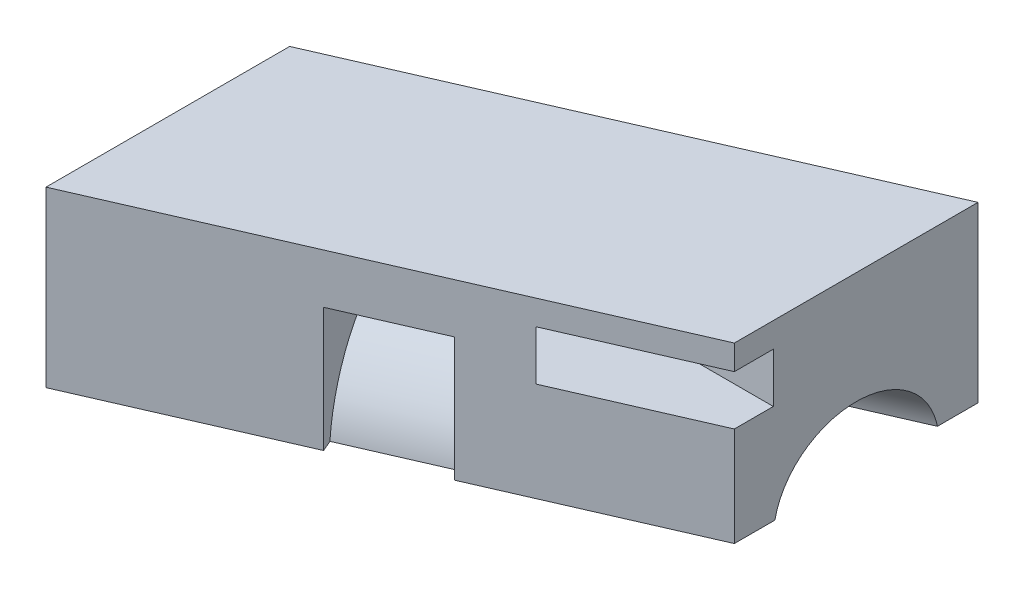
SolidWorks part; units mm, degrees
ref_plane "Front Plane" through (0, 0, 0) normal (0, 0, 1) x (1, 0, 0)
ref_plane "Top Plane" through (0, 0, 0) normal (0, 1, 0) x (1, 0, 0)
ref_plane "Right Plane" through (0, 0, 0) normal (1, 0, 0) x (0, 0, -1)
sketch "Sketch2" plane through (0, 0, 0) normal (0, 1, 0) x (1, 0, 0)
  line L0 (0, 0) -> (-3.6, 8.2486)
  line L1 (-3.6, 8.2486) -> (19.3129, 18.2486)
  line L2 (19.3129, 18.2486) -> (22.9129, 10)
  line L3 (22.9129, 10) -> (0, 0)
  dimension "D1" = 25
  dimension "D2" = 9
  dimension "D3" = 10
extrude "Boss-Extrude2" add sketch "Sketch2" along normal blind 7
sketch "Sketch4" plane through (0, 0, 0) normal (-0.9165, 0, 0.4) x (0.4, 0, 0.9165)
  line L1 (-9, 4.5) -> (0, 4.5) construction
  line L2 (-9, 7) -> (-9, 0) construction
  line L4 (0, 7) -> (0, 0) construction
  line L6 (-9, 7) -> (0, 7) construction
  line L7 (-7.5, 7) -> (-1.5, 7)
  arc A0 (-7.5, 7) -> (-1.5, 7) centre (-4.5, 7.55) ccw
  dimension "D1" = 1.5
  dimension "D2" = 2.5
  dimension "D3" = 1.5
extrude "Cut-Extrude4" cut sketch "Sketch4" against normal up to surface (25 mm away) up to face at (21.1129, 3.5, -14.1243)
ref_plane "Plane1" through (11.4564, 0, -5) normal (0.9165, 0, -0.4) x (-0.4, 0, -0.9165)
sketch "Sketch8" plane through (11.4564, 0, -5) normal (0.9165, 0, -0.4) x (-0.4, 0, -0.9165)
  line L0 (9, 7) -> (9, 0) construction
  line L1 (0, 7) -> (0, 0) construction
  line L2 (0.4875, 7) -> (0, 7)
  line L3 (0, 7) -> (0, 2)
  line L4 (0, 7) -> (1.5, 7) construction
  line L5 (7.5, 7) -> (9, 7) construction
  line L6 (8.5125, 7) -> (9, 7)
  line L7 (9, 7) -> (9, 2)
  line L8 (0, 2) -> (9, 2)
  line L9 (4.5, 3.5) -> (9, 3.5) construction
  arc A0 (8.5125, 7) -> (0.4875, 7) centre (4.5, 7.55) cw
  dimension "D1" = 4.05
  dimension "D2" = 1.5
extrude "Cut-Extrude7" cut sketch "Sketch8" against normal blind 4
sketch "Sketch6" plane through (0, 0, 0) normal (1, 0, 0) x (0, 0, -1)
  line L1 (6, 1) -> (10, 1)
  line L2 (6, 1) -> (6, 3)
  line L3 (6, 3) -> (10, 3)
  line L4 (10, 1) -> (10, 3)
  line L8 (0, 7) -> (0, 0) construction
  line L13 (0, 0) -> (10, 0) construction
  dimension "D1" = 1
  dimension "D2" = 2
  dimension "D3" = 4
  dimension "D4" = 6
extrude "Cut-Extrude5" cut sketch "Sketch6" against normal through all and the other way through all
sketch "Sketch12" plane through (0, 0, 0) normal (0, 1, 0) x (1, 0, 0)
  line L0 (22.9129, 8.4288) -> (22.9129, 18.2486)
  line L1 (22.9129, 18.2486) -> (19.3129, 18.2486)
  line L2 (19.3129, 18.2486) -> (19.3129, 8.4288)
  line L3 (19.3129, 8.4288) -> (22.9129, 8.4288)
  line L4 (22.9129, 10) -> (13.7477, 6) construction
extrude "Cut-Extrude10" cut sketch "Sketch12" along normal through all
sketch "Sketch13" plane through (0, 0, 0) normal (0, 1, 0) x (1, 0, 0)
  line L0 (0, 0) -> (0, 9.8198)
  line L1 (0, 9.8198) -> (-3.6, 9.8198)
  line L2 (-3.6, 9.8198) -> (-3.6, 0)
  line L3 (-3.6, 0) -> (0, 0)
  line L4 (-3.6, 8.2486) -> (0.4129, 10) construction
extrude "Cut-Extrude11" cut sketch "Sketch13" along normal through all
mirror "Mirror9" about plane through (0, 0, 0) normal (0, -1, 0) of bodies 112
delete or keep bodies "Body-Delete/Keep 1" type delete bodies bodies 112
